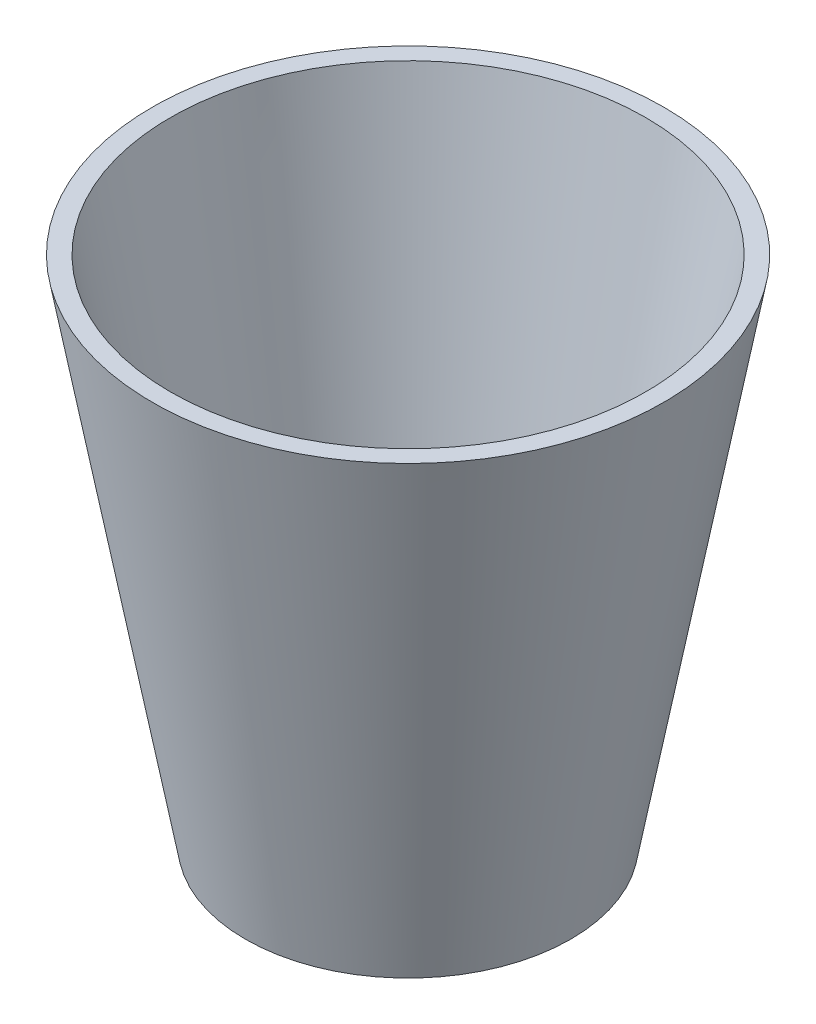
SolidWorks part; units mm, degrees
material "ABS"
ref_plane "Plano frontal" through (0, 0, 0) normal (0, 0, 1) x (1, 0, 0)
ref_plane "Plano superior" through (0, 0, 0) normal (0, 1, 0) x (1, 0, 0)
ref_plane "Plano direito" through (0, 0, 0) normal (1, 0, 0) x (0, 0, -1)
sketch "Esboço1" plane through (0, 0, 0) normal (0, 0, 1) x (1, 0, 0)
  line L0 (0, 0) -> (0, 71.2947) construction
  line L1 (0, 0) -> (17.5, 0)
  line L2 (17.5, 0) -> (27.5, 55)
  line L3 (0, 0.9937) -> (15.639, 1.4415)
  line L4 (15.639, 1.4415) -> (25.5575, 55)
  line L5 (25.5575, 55) -> (27.5, 55)
  line L6 (0, 0) -> (0, 0.9937)
  point P13 (20.5983, 28.2207)
  dimension "D1" = 35
  dimension "D2" = 55
  dimension "D3" = 55
  dimension "D4" = 2
revolve "Revolução1" add sketch "Esboço1" angle 360 about L0
